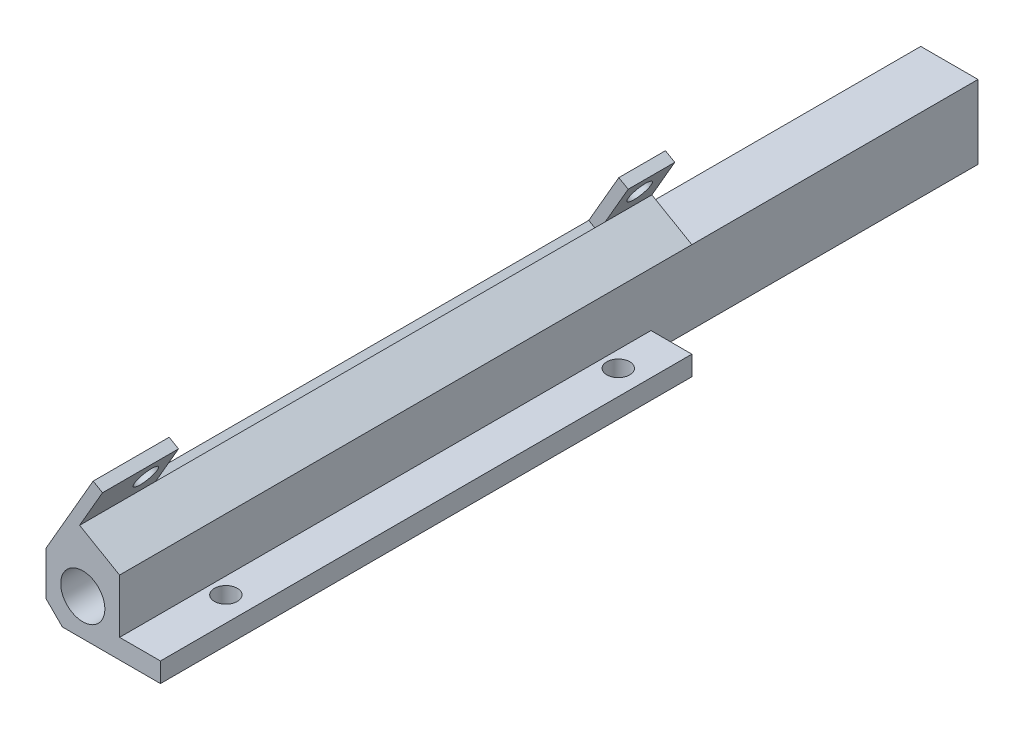
SolidWorks part; units mm, degrees
other "Markup1"
sketch "Sketch28" plane through (0, 0, 0) normal (0, 0, 1) x (1, 0, 0)
sketch "Sketch29" plane through (0, 0, 0) normal (0, 0, 1) x (1, 0, 0)
sketch "Sketch32" plane through (0, 0, 0) normal (0, 0, 1) x (1, 0, 0)
ref_plane "Front Plane" through (0, 0, 0) normal (0, 0, 1) x (1, 0, 0)
ref_plane "Top Plane" through (0, 0, 0) normal (0, 1, 0) x (1, 0, 0)
ref_plane "Right Plane" through (0, 0, 0) normal (1, 0, 0) x (0, 0, -1)
sketch "Sketch1" plane through (0, 0, 0) normal (0, 1, 0) x (1, 0, 0)
  line L1 (0, 0) -> (77.47, 0)
  line L2 (0, 0) -> (0, 133.35)
  line L3 (0, 133.35) -> (77.47, 133.35)
  line L4 (77.47, 0) -> (77.47, 133.35)
  dimension "D1" = 77.47
  dimension "D2" = 133.35
extrude "Boss-Extrude1" add sketch "Sketch1" along normal blind 11.43
sketch "Sketch2" plane through (0, 0, 0) normal (0, 0, 1) x (1, 0, 0)
  line L0 (5.715, 5.715) -> (71.755, 5.715) construction
  line L1 (38.735, 11.43) -> (38.735, 0) construction
  line L2 (0, 11.43) -> (77.47, 11.43) construction
  line L3 (0, 0) -> (77.47, 0) construction
  circle A0 centre (5.715, 5.715) radius 3.429
  circle A1 centre (71.755, 5.715) radius 3.429
  point P10 (38.735, 5.715)
  dimension "D1" = 6.858
  dimension "D2" = 66.04
extrude "Cut-Extrude1" cut sketch "Sketch2" against normal through all
sketch "Sketch3" plane through (0, 11.43, 0) normal (0, 1, 0) x (1, 0, 0)
  line L0 (11.43, 133.35) -> (11.43, 95.25)
  line L1 (77.47, 133.35) -> (0, 133.35) construction
  line L2 (11.43, 133.35) -> (66.04, 133.35)
  line L3 (66.04, 133.35) -> (66.04, 95.25)
  line L4 (53.34, 82.55) -> (24.13, 82.55)
  line L5 (0, 133.35) -> (0, 0) construction
  arc A0 (66.04, 95.25) -> (53.34, 82.55) centre (53.34, 95.25) cw
  arc A1 (24.13, 82.55) -> (11.43, 95.25) centre (24.13, 95.25) cw
  point P10 (38.735, 133.35)
  dimension "D1" = 12.7
  dimension "D2" = 11.43
  dimension "D3" = 50.8
extrude "Cut-Extrude2" cut sketch "Sketch3" against normal through all
sketch "Sketch4" plane through (0, 0, -133.35) normal (0, 0, -1) x (-1, 0, 0)
  line L0 (-11.43, 0) -> (-11.43, 11.43) construction
  line L1 (-66.04, 11.43) -> (-11.43, 11.43)
  line L2 (-66.04, 11.43) -> (-66.04, 5.08)
  line L3 (-66.04, 5.08) -> (-11.43, 5.08)
  line L4 (-11.43, 11.43) -> (-11.43, 5.08)
  line L5 (-11.43, 0) -> (0, 0) construction
  dimension "D1" = 5.08
extrude "Cut-Extrude3" cut sketch "Sketch4" against normal through all
chamfer "Chamfer1" distance 2.54 angle 45 4 edges at (0, 0, -66.675) (0, 11.43, -66.675) (77.47, 0, -66.675) (77.47, 11.43, -66.675)
sketch "Sketch5" plane through (0, 11.43, 0) normal (0, 1, 0) x (1, 0, 0)
  line L0 (11.43, 95.25) -> (11.43, 82.55)
  line L1 (11.43, 0) -> (11.43, 95.25) construction
  line L2 (11.43, 82.55) -> (77.47, 82.55)
  line L3 (77.47, 133.35) -> (77.47, 0) construction
  line L4 (77.47, 82.55) -> (77.47, 133.35)
  line L8 (24.13, 82.55) -> (53.34, 82.55) construction
  line L9 (77.47, 133.35) -> (11.43, 133.35)
  line L10 (11.43, 133.35) -> (11.43, 95.25)
extrude "Cut-Extrude4" cut sketch "Sketch5" against normal through all
sketch "Sketch6" plane through (0, 11.43, 0) normal (0, 1, 0) x (1, 0, 0)
  line L0 (24.13, 82.55) -> (24.13, 0)
  line L1 (11.43, 82.55) -> (66.04, 82.55) construction
  line L2 (66.04, 0) -> (11.43, 0) construction
  line L3 (24.13, 0) -> (77.47, 0)
  line L4 (77.47, 0) -> (77.47, 82.55)
  line L5 (77.47, 82.55) -> (24.13, 82.55)
  line L6 (11.43, 0) -> (11.43, 82.55) construction
  dimension "D1" = 12.7
extrude "Cut-Extrude5" cut sketch "Sketch6" against normal through all
sketch "Sketch7" plane through (0, 5.08, 0) normal (0, 1, 0) x (1, 0, 0)
  line L0 (11.43, 82.55) -> (24.13, 82.55) construction
  line L1 (11.43, 0) -> (11.43, 82.55) construction
  circle A0 centre (13.97, 74.93) radius 1.778
  circle A1 centre (13.97, 13.97) radius 1.778
  dimension "D1" = 3.556
  dimension "D2" = 7.62
  dimension "D3" = 68.58
  dimension "D4" = 2.54
extrude "Hole Cuts 1" cut sketch "Sketch7" against normal through all
sketch "Sketch17" plane through (0, 0, 0) normal (0, 0, 1) x (1, 0, 0)
  line L0 (0, 8.89) -> (0, 11.8699)
  line L1 (0, 11.8699) -> (5.588, 21.5486)
  line L2 (5.588, 21.5486) -> (8.8517, 19.6643)
  line L3 (8.8517, 19.6643) -> (5.9307, 14.605)
  line L4 (5.9307, 14.605) -> (11.43, 11.43)
  line L5 (0, 8.89) -> (0, 2.54) construction
  line L6 (11.43, 11.43) -> (2.54, 11.43)
  line L7 (2.54, 11.43) -> (0, 8.89)
  dimension "D1" = 11.176
  dimension "D2" = 5.842
  dimension "D3" = 6.35
  dimension "D4" = 60
extrude "Boss-Extrude5" add sketch "Sketch17" against normal blind 88.9
sketch "Sketch18" plane through (0, 0, 0) normal (0, 0, 1) x (1, 0, 0)
  line L0 (2.54, 0) -> (17.78, 0) construction
  line L1 (2.54, 0) -> (24.13, 0) construction
  line L2 (11.43, 5.08) -> (11.43, 11.43) construction
  line L3 (17.78, 0) -> (24.13, 0)
  line L4 (24.13, 0) -> (24.13, 5.08)
  line L5 (24.13, 5.08) -> (17.78, 5.08)
  line L6 (24.13, 5.08) -> (11.43, 5.08) construction
  line L7 (17.78, 5.08) -> (17.78, 0)
  dimension "D1" = 6.35
extrude "Cut-Extrude13" cut sketch "Sketch18" against normal blind 76.2
sketch "Sketch19" plane through (-1.8761, 1.0832, 0) normal (0.866, -0.5, 0) x (0, 0, -1)
  line L0 (0, 15.6137) -> (0, 21.4557) construction
  line L1 (88.9, 15.6137) -> (0, 15.6137) construction
  line L4 (88.9, 15.6137) -> (88.9, 21.4557) construction
  circle A0 centre (8.382, 19.4237) radius 1.778
  circle A1 centre (85.09, 19.4237) radius 1.778
  dimension "D1" = 3.556
  dimension "D3" = 76.708
  dimension "D2" = 8.382
  dimension "D4" = 3.81
  dimension "D5" = 3.81
extrude "Hole Cuts 2" cut sketch "Sketch19" against normal up to next
sketch "Sketch20" plane through (-5.1398, 2.9675, 0) normal (-0.866, 0.5, 0) x (0, 0, 1)
  line L1 (-88.9, 21.4557) -> (0, 21.4557)
  line L2 (-88.9, 21.4557) -> (-88.9, 10.2797)
  line L3 (-88.9, 10.2797) -> (0, 10.2797)
  line L4 (0, 21.4557) -> (0, 10.2797)
extrude "Cut-Extrude16" cut sketch "Sketch20" against normal blind 1.27
sketch "Sketch31" plane through (0, 0, 0) normal (0, 0, 1) x (1, 0, 0)
  line L0 (-994.285, 5.715) -> (49005.715, 5.715) construction
  line L1 (15.5782, 22.7985) -> (5.715, 5.715) construction
  line L2 (8.14, 20.0752) -> (12.5394, 17.5352)
  line L3 (8.14, 20.0752) -> (5.219, 15.0159)
  line L4 (12.5394, 17.5352) -> (9.6184, 12.4759)
  line L5 (5.219, 15.0159) -> (9.6184, 12.4759)
  line L6 (11.43, 11.43) -> (5.9307, 14.605) construction
  line L7 (8.8517, 19.6643) -> (6.6879, 20.9136) construction
  circle A0 centre (5.715, 5.715) radius 3.429 construction
  dimension "D1" = 60
  dimension "D2" = 5.08
extrude "Cut-Extrude22" cut sketch "Sketch31" against normal through all
sketch "Sketch22" plane through (0, 5.08, 0) normal (0, 1, 0) x (1, 0, 0)
  line L1 (17.78, 0) -> (11.43, 0)
  line L2 (17.78, 0) -> (17.78, 82.55)
  line L3 (17.78, 82.55) -> (11.43, 82.55)
  line L4 (11.43, 0) -> (11.43, 82.55)
extrude "Cut-Extrude18" cut sketch "Sketch22" against normal blind 2.032
sketch "Sketch23" plane through (10.7278, 18.5812, 0) normal (0.5, 0.866, 0) x (0.866, -0.5, 0)
  line L0 (-2.9882, 88.9) -> (-2.9882, 0) construction
  line L1 (-4.665, 88.9) -> (-2.9882, 88.9)
  line L2 (-4.665, 88.9) -> (-4.665, 0)
  line L3 (-4.665, 0) -> (-2.9882, 0)
  line L4 (-2.9882, 88.9) -> (-2.9882, 0)
  line L5 (-2.9882, 0) -> (-4.665, 0) construction
extrude "Boss-Extrude6" add sketch "Sketch23" along normal blind 1.27
sketch "Sketch24" plane through (-2.5878, 1.4941, 0) normal (0.866, -0.5, 0) x (0, 0, -1)
  line L0 (0, 22.7257) -> (88.9, 22.7257) construction
  line L1 (11.811, 22.7257) -> (81.661, 22.7257)
  line L2 (11.811, 22.7257) -> (11.811, 13.3912)
  line L3 (11.811, 13.3912) -> (81.661, 13.3912)
  line L4 (81.661, 22.7257) -> (81.661, 13.3912)
  line L6 (8.382, 19.4237) -> (85.09, 19.4237) construction
  point P8 (46.736, 19.4237)
  point P9 (46.736, 22.7257)
  dimension "D1" = 69.85
  dimension "D2" = 9.3345
extrude "Cut-Extrude19" cut sketch "Sketch24" against normal up to next
sketch "Sketch25" plane through (5.1398, 8.9025, 0) normal (0.5, 0.866, 0) x (0.866, -0.5, 0)
  line L1 (-5.935, 88.9) -> (-4.665, 88.9)
  line L2 (-5.935, 88.9) -> (-5.935, 0)
  line L3 (-5.935, 0) -> (-4.665, 0)
  line L4 (-4.665, 88.9) -> (-4.665, 0)
extrude "Cut-Extrude20" cut sketch "Sketch25" against normal up to next
sketch "Sketch26" plane through (0, 5.08, 0) normal (0, 1, 0) x (1, 0, 0)
  line L1 (17.78, 82.55) -> (24.13, 82.55)
  line L2 (17.78, 82.55) -> (17.78, 76.2)
  line L3 (17.78, 76.2) -> (24.13, 76.2)
  line L4 (24.13, 82.55) -> (24.13, 76.2)
extrude "Cut-Extrude21" cut sketch "Sketch26" against normal up to next
